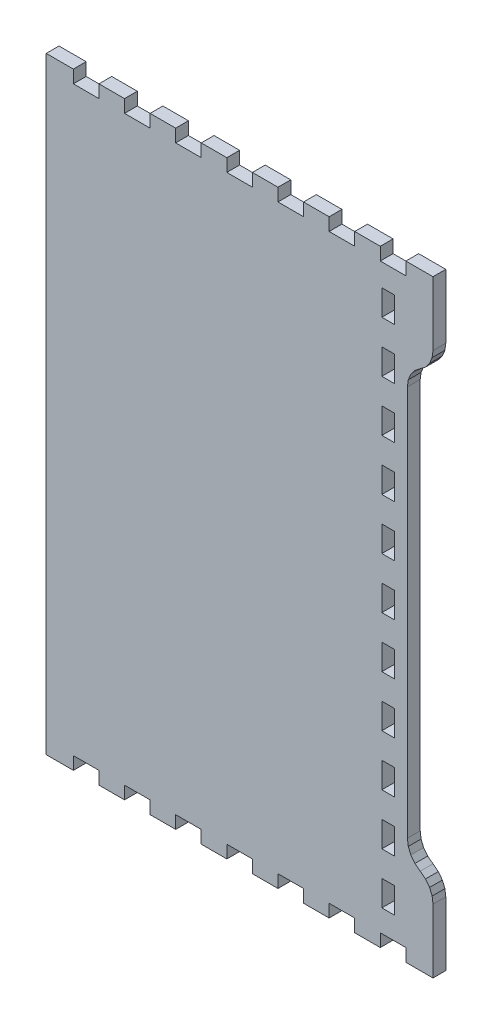
SolidWorks part; units mm, degrees
ref_plane "Front Plane" through (0, 0, 0) normal (0, 0, 1) x (1, 0, 0)
ref_plane "Top Plane" through (0, 0, 0) normal (0, 1, 0) x (1, 0, 0)
ref_plane "Right Plane" through (0, 0, 0) normal (1, 0, 0) x (0, 0, -1)
sketch "Model" plane through (0, 0, 0) normal (0, 0, 1) x (1, 0, 0)
  line L797 (1288.6101, 22.8602) -> (1300.746, 22.8602)
  line L798 (1300.746, 22.8602) -> (1300.746, 28.5752)
  line L799 (1300.746, 28.5752) -> (1312.1767, 28.5752)
  line L800 (1312.1767, 28.5752) -> (1312.1767, 22.8602)
  line L801 (1312.1767, 22.8602) -> (1323.6074, 22.8602)
  line L802 (1323.6074, 22.8602) -> (1323.6074, 28.5752)
  line L803 (1323.6074, 28.5752) -> (1335.0381, 28.5752)
  line L804 (1335.0381, 28.5752) -> (1335.0381, 22.8602)
  line L805 (1335.0381, 22.8602) -> (1346.4653, 22.8602)
  line L806 (1346.4653, 22.8602) -> (1346.4653, 28.5752)
  line L807 (1346.4653, 28.5752) -> (1357.896, 28.5752)
  line L808 (1357.896, 28.5752) -> (1357.896, 22.8602)
  line L809 (1357.896, 22.8602) -> (1369.3268, 22.8602)
  line L810 (1369.3268, 22.8602) -> (1369.3268, 28.5752)
  line L811 (1369.3268, 28.5752) -> (1380.7575, 28.5752)
  line L812 (1380.7575, 28.5752) -> (1380.7575, 22.8602)
  line L813 (1380.7575, 22.8602) -> (1392.1882, 22.8602)
  line L814 (1392.1882, 22.8602) -> (1392.1882, 28.5752)
  line L815 (1392.1882, 28.5752) -> (1403.6154, 28.5752)
  line L816 (1403.6154, 28.5752) -> (1403.6154, 22.8602)
  line L817 (1403.6154, 22.8602) -> (1415.0461, 22.8602)
  line L818 (1415.0461, 22.8602) -> (1415.0461, 28.5752)
  line L819 (1415.0461, 28.5752) -> (1426.4768, 28.5752)
  line L820 (1426.4768, 28.5752) -> (1426.4768, 22.8602)
  line L821 (1426.4768, 22.8602) -> (1437.9075, 22.8602)
  line L822 (1437.9075, 22.8602) -> (1437.9075, 28.5752)
  line L823 (1437.9075, 28.5752) -> (1449.3383, 28.5752)
  line L824 (1449.3383, 28.5752) -> (1449.3383, 22.8602)
  line L825 (1449.3383, 22.8602) -> (1461.4706, 22.8602)
  line L826 (1461.4706, 22.8602) -> (1461.4706, 28.5752)
  line L827 (1461.4706, 28.5752) -> (1461.4706, 51.4354)
  line L828 (1461.4706, 51.4354) -> (1461.0812, 54.3934)
  line L829 (1461.0812, 54.3934) -> (1459.9399, 57.1504)
  line L830 (1459.9399, 57.1504) -> (1458.1239, 59.5176)
  line L831 (1458.1239, 59.5176) -> (1455.7552, 61.3344)
  line L832 (1455.7552, 61.3344) -> (1453.3896, 63.1505)
  line L833 (1453.3896, 63.1505) -> (1451.5741, 65.5172)
  line L834 (1451.5741, 65.5172) -> (1450.4296, 68.2743)
  line L835 (1450.4296, 68.2743) -> (1450.0398, 71.2322)
  line L836 (1450.0398, 71.2322) -> (1450.0398, 245.9182)
  line L837 (1450.0398, 245.9182) -> (1450.4296, 248.8763)
  line L838 (1450.4296, 248.8763) -> (1451.5741, 251.6332)
  line L839 (1451.5741, 251.6332) -> (1453.3896, 254.0001)
  line L840 (1453.3896, 254.0001) -> (1455.7552, 255.8164)
  line L841 (1455.7552, 255.8164) -> (1458.1239, 257.6331)
  line L842 (1458.1239, 257.6331) -> (1459.9399, 260.0004)
  line L843 (1459.9399, 260.0004) -> (1461.0812, 262.7573)
  line L844 (1461.0812, 262.7573) -> (1461.4706, 265.7154)
  line L845 (1461.4706, 265.7154) -> (1461.4706, 288.5754)
  line L846 (1461.4706, 288.5754) -> (1461.4706, 294.2904)
  line L847 (1461.4706, 294.2904) -> (1449.3383, 294.2904)
  line L848 (1449.3383, 294.2904) -> (1449.3383, 288.5754)
  line L849 (1449.3383, 288.5754) -> (1437.9075, 288.5754)
  line L850 (1437.9075, 288.5754) -> (1437.9075, 294.2904)
  line L851 (1437.9075, 294.2904) -> (1426.4768, 294.2904)
  line L852 (1426.4768, 294.2904) -> (1426.4768, 288.5754)
  line L853 (1426.4768, 288.5754) -> (1415.0461, 288.5754)
  line L854 (1415.0461, 288.5754) -> (1415.0461, 294.2904)
  line L855 (1415.0461, 294.2904) -> (1403.6154, 294.2904)
  line L856 (1403.6154, 294.2904) -> (1403.6154, 288.5754)
  line L857 (1403.6154, 288.5754) -> (1392.1882, 288.5754)
  line L858 (1392.1882, 288.5754) -> (1392.1882, 294.2904)
  line L859 (1392.1882, 294.2904) -> (1380.7575, 294.2904)
  line L860 (1380.7575, 294.2904) -> (1380.7575, 288.5754)
  line L861 (1380.7575, 288.5754) -> (1369.3268, 288.5754)
  line L862 (1369.3268, 288.5754) -> (1369.3268, 294.2904)
  line L863 (1369.3268, 294.2904) -> (1357.896, 294.2904)
  line L864 (1357.896, 294.2904) -> (1357.896, 288.5754)
  line L865 (1357.896, 288.5754) -> (1346.4653, 288.5754)
  line L866 (1346.4653, 288.5754) -> (1346.4653, 294.2904)
  line L867 (1346.4653, 294.2904) -> (1335.0381, 294.2904)
  line L868 (1335.0381, 294.2904) -> (1335.0381, 288.5754)
  line L869 (1335.0381, 288.5754) -> (1323.6074, 288.5754)
  line L870 (1323.6074, 288.5754) -> (1323.6074, 294.2904)
  line L871 (1323.6074, 294.2904) -> (1312.1767, 294.2904)
  line L872 (1312.1767, 294.2904) -> (1312.1767, 288.5754)
  line L873 (1312.1767, 288.5754) -> (1300.746, 288.5754)
  line L874 (1300.746, 288.5754) -> (1300.746, 294.2904)
  line L875 (1300.746, 294.2904) -> (1288.6101, 294.2904)
  line L876 (1288.6101, 294.2904) -> (1288.6101, 288.5754)
  line L877 (1288.6101, 288.5754) -> (1288.6101, 28.5752)
  line L878 (1288.6101, 28.5752) -> (1288.6101, 22.8602)
  line L879 (1444.328, 44.2751) -> (1444.328, 38.5601)
  line L880 (1444.328, 38.5601) -> (1438.6127, 38.5601)
  line L881 (1438.6127, 38.5601) -> (1438.6127, 49.9901)
  line L882 (1438.6127, 49.9901) -> (1444.328, 49.9901)
  line L883 (1444.328, 49.9901) -> (1444.328, 44.2751)
  line L884 (1444.328, 67.1351) -> (1444.328, 61.4201)
  line L885 (1444.328, 61.4201) -> (1438.6127, 61.4201)
  line L886 (1438.6127, 61.4201) -> (1438.6127, 72.8501)
  line L887 (1438.6127, 72.8501) -> (1444.328, 72.8501)
  line L888 (1444.328, 72.8501) -> (1444.328, 67.1351)
  line L889 (1444.328, 89.9951) -> (1444.328, 84.2801)
  line L890 (1444.328, 84.2801) -> (1438.6127, 84.2801)
  line L891 (1438.6127, 84.2801) -> (1438.6127, 95.7101)
  line L892 (1438.6127, 95.7101) -> (1444.328, 95.7101)
  line L893 (1444.328, 95.7101) -> (1444.328, 89.9951)
  line L894 (1444.328, 112.8552) -> (1444.328, 107.1402)
  line L895 (1444.328, 107.1402) -> (1438.6127, 107.1402)
  line L896 (1438.6127, 107.1402) -> (1438.6127, 118.5702)
  line L897 (1438.6127, 118.5702) -> (1444.328, 118.5702)
  line L898 (1444.328, 118.5702) -> (1444.328, 112.8552)
  line L899 (1444.328, 135.7152) -> (1444.328, 130.0002)
  line L900 (1444.328, 130.0002) -> (1438.6127, 130.0002)
  line L901 (1438.6127, 130.0002) -> (1438.6127, 141.4302)
  line L902 (1438.6127, 141.4302) -> (1444.328, 141.4302)
  line L903 (1444.328, 141.4302) -> (1444.328, 135.7152)
  line L904 (1444.328, 158.5752) -> (1444.328, 152.8602)
  line L905 (1444.328, 152.8602) -> (1438.6127, 152.8602)
  line L906 (1438.6127, 152.8602) -> (1438.6127, 164.2902)
  line L907 (1438.6127, 164.2902) -> (1444.328, 164.2902)
  line L908 (1444.328, 164.2902) -> (1444.328, 158.5752)
  line L909 (1444.328, 181.4352) -> (1444.328, 175.7202)
  line L910 (1444.328, 175.7202) -> (1438.6127, 175.7202)
  line L911 (1438.6127, 175.7202) -> (1438.6127, 187.1503)
  line L912 (1438.6127, 187.1503) -> (1444.328, 187.1503)
  line L913 (1444.328, 187.1503) -> (1444.328, 181.4352)
  line L914 (1444.328, 204.2953) -> (1444.328, 198.5803)
  line L915 (1444.328, 198.5803) -> (1438.6127, 198.5803)
  line L916 (1438.6127, 198.5803) -> (1438.6127, 210.0103)
  line L917 (1438.6127, 210.0103) -> (1444.328, 210.0103)
  line L918 (1444.328, 210.0103) -> (1444.328, 204.2953)
  line L919 (1444.328, 227.1553) -> (1444.328, 221.4403)
  line L920 (1444.328, 221.4403) -> (1438.6127, 221.4403)
  line L921 (1438.6127, 221.4403) -> (1438.6127, 232.8703)
  line L922 (1438.6127, 232.8703) -> (1444.328, 232.8703)
  line L923 (1444.328, 232.8703) -> (1444.328, 227.1553)
  line L924 (1444.328, 250.0153) -> (1444.328, 244.3003)
  line L925 (1444.328, 244.3003) -> (1438.6127, 244.3003)
  line L926 (1438.6127, 244.3003) -> (1438.6127, 255.7303)
  line L927 (1438.6127, 255.7303) -> (1444.328, 255.7303)
  line L928 (1444.328, 255.7303) -> (1444.328, 250.0153)
  line L929 (1444.328, 272.8754) -> (1444.328, 267.1603)
  line L930 (1444.328, 267.1603) -> (1438.6127, 267.1603)
  line L931 (1438.6127, 267.1603) -> (1438.6127, 278.5904)
  line L932 (1438.6127, 278.5904) -> (1444.328, 278.5904)
  line L933 (1444.328, 278.5904) -> (1444.328, 272.8754)
extrude "Boss-Extrude1" add sketch "Model" along normal blind 5.715
